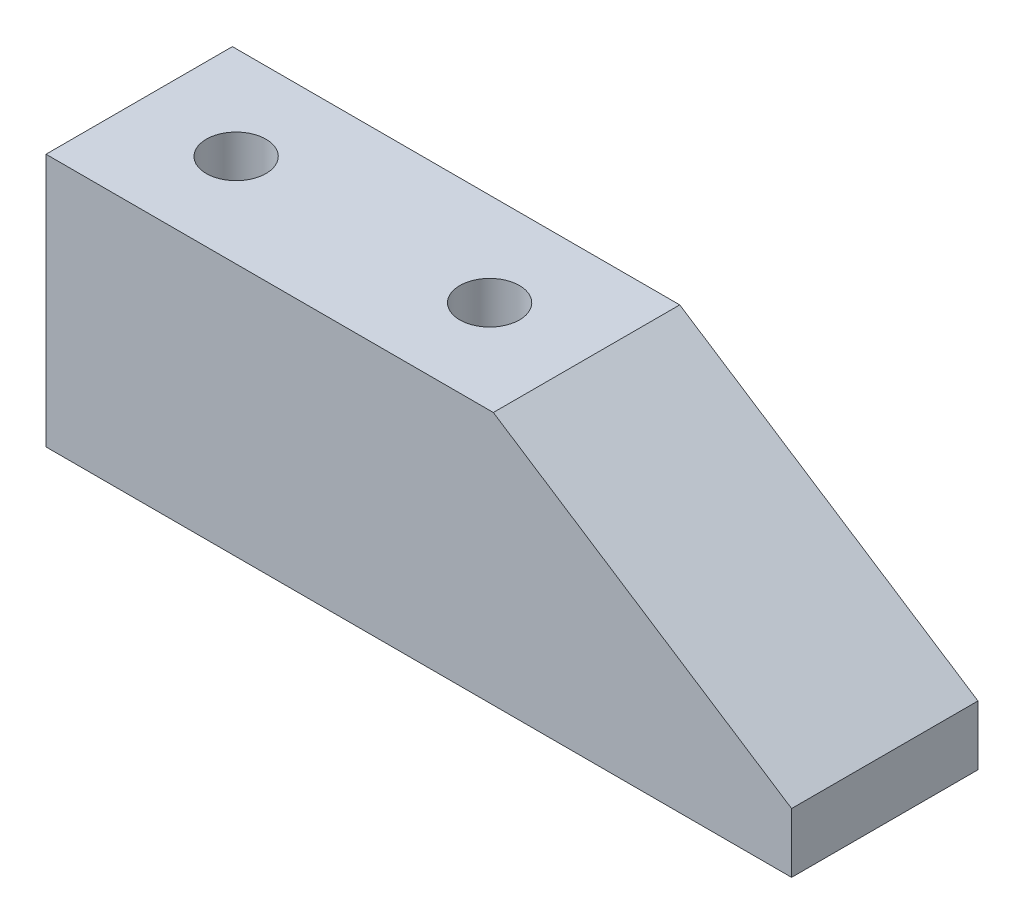
SolidWorks part; units mm, degrees
ref_plane "Front Plane" through (0, 0, 0) normal (0, 0, 1) x (1, 0, 0)
ref_plane "Top Plane" through (0, 0, 0) normal (0, 1, 0) x (1, 0, 0)
ref_plane "Right Plane" through (0, 0, 0) normal (1, 0, 0) x (0, 0, -1)
sketch "Sketch1" plane through (0, 0, 0) normal (0, 0, 1) x (1, 0, 0)
  line L4 (0, 0) -> (0, -17)
  line L5 (0, -17) -> (50, -17)
  line L6 (50, -17) -> (50, -13)
  line L7 (50, -13) -> (30, 0)
  line L8 (30, 0) -> (0, 0)
  dimension "D1" = 50
  dimension "D2" = 17
  dimension "D3" = 30
  dimension "D4" = 4
extrude "Boss-Extrude1" add sketch "Sketch1" along normal blind 12.5
sketch "Sketch2" plane through (0, 0, 0) normal (0, 1, 0) x (1, 0, 0)
  line L0 (15, 4.1508) -> (15, -17.8618) construction
  line L1 (0, -12.5) -> (0, 0) construction
  line L2 (30, 0) -> (0, 0) construction
  circle A0 centre (6.5, -6.25) radius 2
  circle A1 centre (23.5, -6.25) radius 2
  dimension "D2" = 4
  dimension "D1" = 15
  dimension "D3" = 8.5
  dimension "D4" = 6.25
extrude "Cut-Extrude1" cut sketch "Sketch2" against normal blind 8
